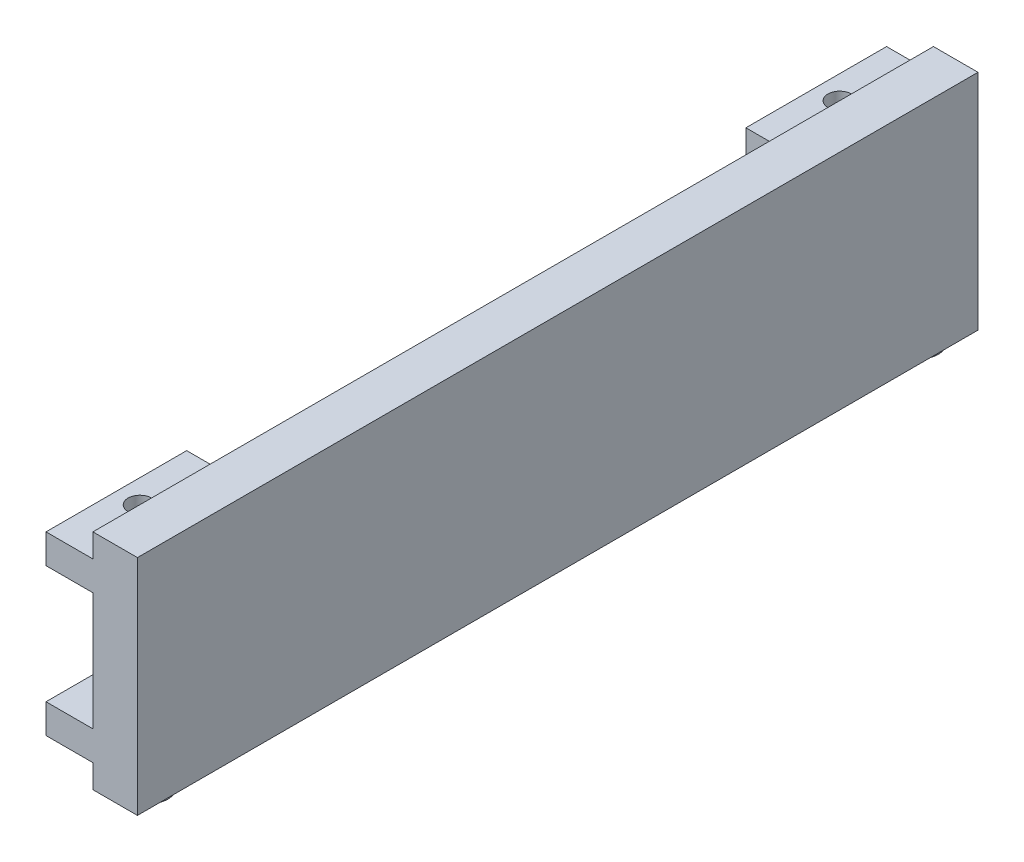
SolidWorks part; units mm, degrees
ref_plane "Front Plane" through (0, 0, 0) normal (0, 0, 1) x (1, 0, 0)
ref_plane "Top Plane" through (0, 0, 0) normal (0, 1, 0) x (1, 0, 0)
ref_plane "Right Plane" through (0, 0, 0) normal (1, 0, 0) x (0, 0, -1)
sketch "Sketch1" plane through (0, 0, 0) normal (0, 1, 0) x (1, 0, 0)
  line L1 (1.5403, -3.0806) -> (39.5403, -3.0806)
  line L2 (1.5403, -3.0806) -> (1.5403, -720.0806)
  line L3 (1.5403, -720.0806) -> (39.5403, -720.0806)
  line L4 (39.5403, -3.0806) -> (39.5403, -720.0806)
  dimension "D1" = 717
  dimension "D2" = 38
extrude "Boss-Extrude1" add sketch "Sketch1" along normal blind 190.5
sketch "Sketch3" plane through (1.5403, 0, 0) normal (-1, 0, 0) x (0, 0, 1)
  line L0 (3.0806, 190.5) -> (3.0806, 0) construction
  line L1 (3.0806, 170.5) -> (123.0806, 170.5)
  line L2 (3.0806, 170.5) -> (3.0806, 145.5)
  line L3 (3.0806, 145.5) -> (123.0806, 145.5)
  line L4 (123.0806, 170.5) -> (123.0806, 145.5)
  line L5 (3.0806, 190.5) -> (720.0806, 190.5) construction
  line L6 (3.0806, 45) -> (123.0806, 45)
  line L7 (3.0806, 45) -> (3.0806, 20)
  line L8 (3.0806, 20) -> (123.0806, 20)
  line L9 (123.0806, 45) -> (123.0806, 20)
  line L10 (3.0806, 0) -> (720.0806, 0) construction
  line L11 (361.5806, 190.5) -> (361.5806, 0) construction
  line L12 (720.0806, 20) -> (600.0806, 20)
  line L13 (600.0806, 45) -> (600.0806, 20)
  line L14 (720.0806, 45) -> (600.0806, 45)
  line L15 (720.0806, 45) -> (720.0806, 20)
  line L16 (720.0806, 145.5) -> (600.0806, 145.5)
  line L17 (600.0806, 170.5) -> (600.0806, 145.5)
  line L18 (720.0806, 170.5) -> (600.0806, 170.5)
  line L19 (720.0806, 170.5) -> (720.0806, 145.5)
  dimension "D1" = 120
  dimension "D2" = 120
  dimension "D3" = 25
  dimension "D4" = 25
  dimension "D5" = 20
  dimension "D6" = 20
extrude "Boss-Extrude2" add sketch "Sketch3" along normal blind 40
sketch "Sketch4" plane through (0, 170.5, 0) normal (0, 1, 0) x (1, 0, 0)
  line L0 (-38.4597, -123.0806) -> (-38.4597, -3.0806) construction
  line L1 (-38.4597, -3.0806) -> (1.5403, -3.0806) construction
  line L2 (-38.4597, -600.0806) -> (1.5403, -600.0806) construction
  line L3 (-38.4597, -720.0806) -> (-38.4597, -600.0806) construction
  circle A0 centre (-18.4597, -63.0806) radius 10
  circle A1 centre (-18.4597, -660.0806) radius 10
  dimension "D1" = 20
  dimension "D5" = 20
  dimension "D2" = 20
  dimension "D3" = 60
  dimension "D4" = 60
  dimension "D6" = 20
extrude "Cut-Extrude1" cut sketch "Sketch4" against normal blind 506
sketch "Sketch5" plane through (0, 0, 0) normal (0, -1, 0) x (1, 0, 0)
  line L0 (39.5403, 720.0806) -> (39.5403, 3.0806) construction
  line L1 (1.5403, 720.0806) -> (39.5403, 720.0806) construction
  line L2 (39.5403, 3.0806) -> (1.5403, 3.0806) construction
  circle A0 centre (20.5403, 690.0806) radius 15
  circle A1 centre (20.5403, 33.0806) radius 15
  dimension "D1" = 30
  dimension "D2" = 30
  dimension "D6" = 30
  dimension "D3" = 19
  dimension "D4" = 30
  dimension "D5" = 19
extrude "Boss-Extrude3" add sketch "Sketch5" along normal blind 5
